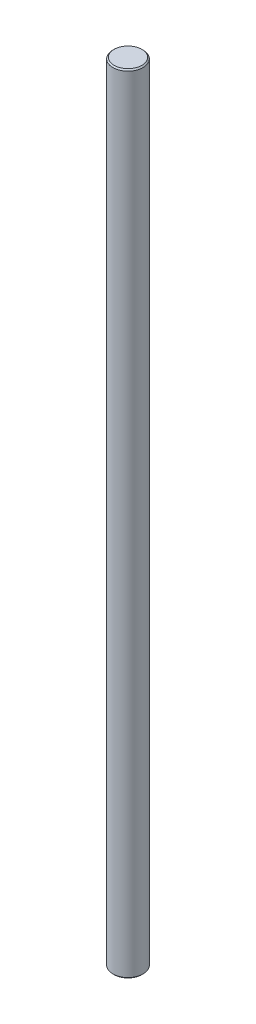
SolidWorks part; units mm, degrees
material "Acero inoxidable al cromo"
ref_plane "Alzado" through (0, 0, 0) normal (0, 0, 1) x (1, 0, 0)
ref_plane "Planta" through (0, 0, 0) normal (0, 1, 0) x (1, 0, 0)
ref_plane "Vista lateral" through (0, 0, 0) normal (1, 0, 0) x (0, 0, -1)
sketch "Croquis1" plane through (0, 0, 0) normal (0, 1, 0) x (1, 0, 0)
  circle A0 centre (0, 0) radius 6
  dimension "D1" = 12
extrude "Saliente-Extruir1" add sketch "Croquis1" along normal blind 312
chamfer "Chaflán1" distance 0.5 angle 45 2 edges at (0, 312, 6) (0, 0, 6)
